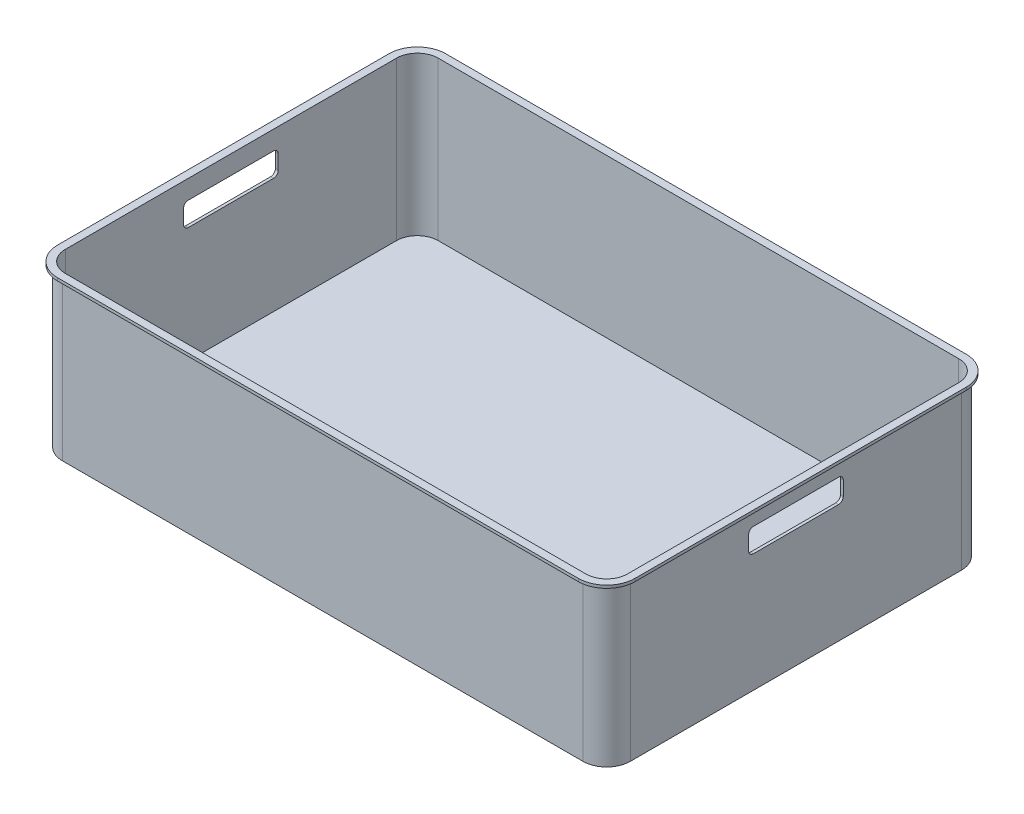
SolidWorks part; units mm, degrees
ref_plane "Front Plane" through (0, 0, 0) normal (0, 0, 1) x (1, 0, 0)
ref_plane "Top Plane" through (0, 0, 0) normal (0, 1, 0) x (1, 0, 0)
ref_plane "Right Plane" through (0, 0, 0) normal (1, 0, 0) x (0, 0, -1)
sketch "Sketch1" plane through (0, 0, 0) normal (0, 1, 0) x (1, 0, 0)
  line L1 (0, 0) -> (600, 0)
  line L2 (0, 0) -> (0, 400)
  line L3 (0, 400) -> (600, 400)
  line L4 (600, 0) -> (600, 400)
extrude "Boss-Extrude1" add sketch "Sketch1" along normal blind 170
fillet "Fillet1" radius 25 4 edges at (0, 85, -400) (600, 85, -400) (600, 85, 0) (0, 85, 0)
shell "Shell1" thickness 3
ref_plane "Plane1" through (0, 170, 0) normal (0, 1, 0) x (1, 0, 0)
sketch "Sketch2" plane through (0, 170, 0) normal (0, 1, 0) x (1, 0, 0)
  line L1 (25, 400) -> (575, 400)
  line L2 (0, 375) -> (0, 25)
  line L3 (25, 0) -> (575, 0)
  line L4 (600, 375) -> (600, 25)
  arc A0 (25, 400) -> (0, 375) centre (25, 375) ccw
  arc A1 (575, 400) -> (600, 375) centre (575, 375) cw
  arc A2 (575, 0) -> (600, 25) centre (575, 25) ccw
  arc A3 (0, 25) -> (25, 0) centre (25, 25) ccw
  dimension "D1" = 25
extrude "Extrude-Thin1" add sketch "Sketch2" against normal blind 3 thin thin type one direction wall 5
ref_plane "Plane3" through (0, 0, 0) normal (-1, 0, 0) x (0, 0, 1)
sketch "Sketch4" plane through (0, 0, 0) normal (-1, 0, 0) x (0, 0, 1)
  line L2 (-200, 150) -> (-155, 150)
  line L3 (-150, 145) -> (-150, 130)
  line L4 (-155, 125) -> (-245, 125)
  line L5 (-250, 130) -> (-250, 145)
  line L6 (-245, 150) -> (-200, 150)
  arc A0 (-150, 130) -> (-155, 125) centre (-155, 130) cw
  arc A1 (-155, 150) -> (-150, 145) centre (-155, 145) cw
  arc A2 (-250, 145) -> (-245, 150) centre (-245, 145) cw
  arc A3 (-245, 125) -> (-250, 130) centre (-245, 130) cw
  dimension "D1" = 5
extrude "Cut-Extrude2" cut sketch "Sketch4" against normal blind 1000 and the other way blind 1000
